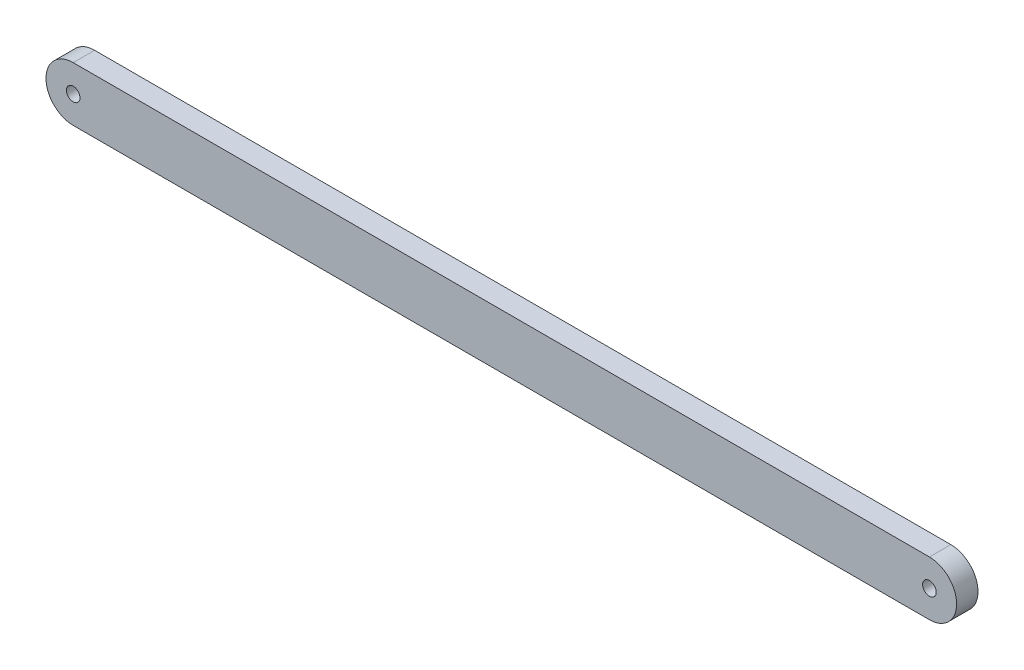
SolidWorks part; units mm, degrees
ref_plane "Front Plane" through (0, 0, 0) normal (0, 0, 1) x (1, 0, 0)
ref_plane "Top Plane" through (0, 0, 0) normal (0, 1, 0) x (1, 0, 0)
ref_plane "Right Plane" through (0, 0, 0) normal (1, 0, 0) x (0, 0, -1)
sketch "Sketch1" plane through (0, 0, 0) normal (0, 0, 1) x (1, 0, 0)
  line L0 (0, 12.7) -> (400, 12.7)
  line L1 (0, -12.7) -> (400, -12.7)
  arc A0 (0, 12.7) -> (0, -12.7) centre (0, 0) ccw
  arc A1 (400, -12.7) -> (400, 12.7) centre (400, 0) ccw
  circle A2 centre (0, 0) radius 3.175
  circle A3 centre (400, 0) radius 3.175
  dimension "D1" = 25.4
  dimension "D3" = 6.35
  dimension "D2" = 400
extrude "Boss-Extrude1" add sketch "Sketch1" along normal blind 10
